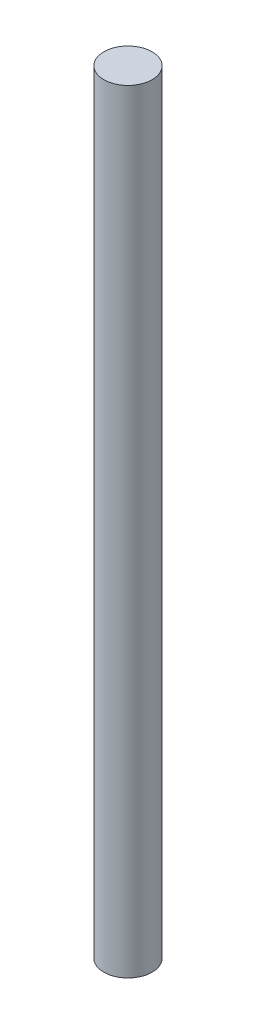
SolidWorks part; units mm, degrees
material "Plain Carbon Steel"
ref_plane "Front Plane" through (0, 0, 0) normal (0, 0, 1) x (1, 0, 0)
ref_plane "Top Plane" through (0, 0, 0) normal (0, 1, 0) x (1, 0, 0)
ref_plane "Right Plane" through (0, 0, 0) normal (1, 0, 0) x (0, 0, -1)
sketch "Sketch1" plane through (0, 0, 0) normal (0, 1, 0) x (1, 0, 0)
  circle A0 centre (0, 0) radius 6.35
  dimension "D1" = 12.7
extrude "Boss-Extrude1" add sketch "Sketch1" along normal mid plane 203.2
